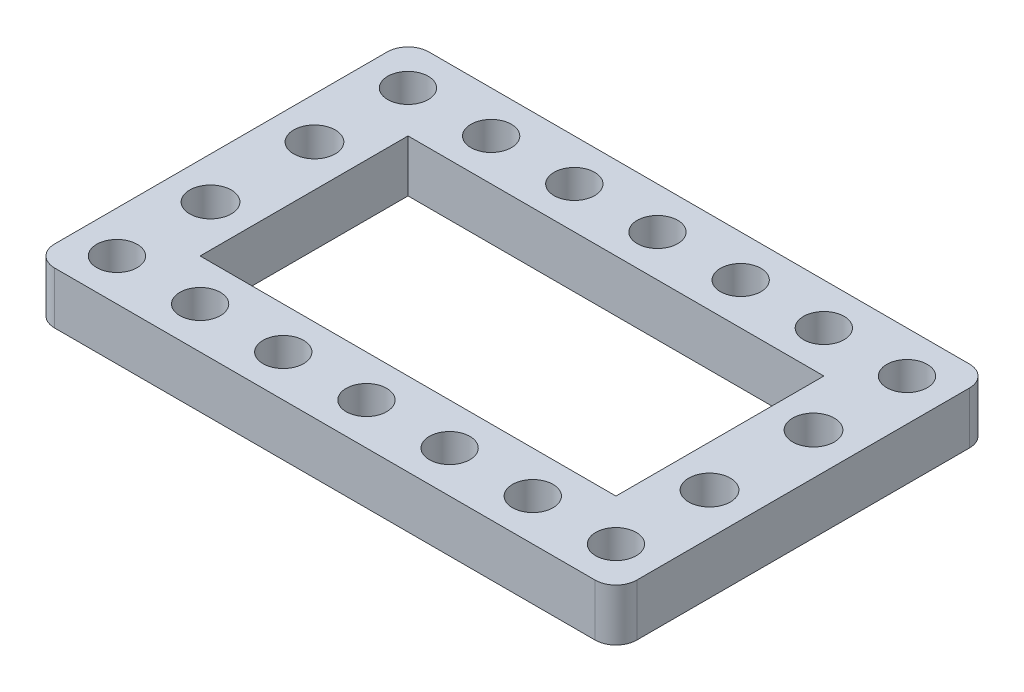
SolidWorks part; units mm, degrees
other "Markup1"
sketch "Sketch6" plane through (78, 5, 36) normal (0.7831, 0.6182, 0.0676) x (0.6216, -0.7756, -0.1096)
ref_plane "Front Plane" through (0, 0, 0) normal (0, 0, 1) x (1, 0, 0)
ref_plane "Top Plane" through (0, 0, 0) normal (0, 1, 0) x (1, 0, 0)
ref_plane "Right Plane" through (0, 0, 0) normal (1, 0, 0) x (0, 0, -1)
sketch "Sketch1" plane through (0, 0, 0) normal (0, 1, 0) x (1, 0, 0)
  line L1 (2, 0) -> (98, 0)
  line L2 (0, -2) -> (0, -34)
  line L3 (2, -36) -> (98, -36)
  line L4 (100, -2) -> (100, -34)
  arc A0 (98, -36) -> (100, -34) centre (98, -34) ccw
  arc A1 (0, -34) -> (2, -36) centre (2, -34) ccw
  arc A2 (2, 0) -> (0, -2) centre (2, -2) ccw
  arc A3 (98, 0) -> (100, -2) centre (98, -2) cw
  point P7 (100, -36)
  point P12 (0, 0)
  point P15 (100, 0)
  dimension "D3" = 2
  dimension "D1" = 100
  dimension "D2" = 36
extrude "Boss-Extrude1" add sketch "Sketch1" along normal blind 5
sketch "Sketch2" plane through (0, 5, 0) normal (0, 1, 0) x (1, 0, 0)
  line L1 (100, -34) -> (100, -2) construction
  line L2 (90, -4.0048) -> (0, -4.0048) construction
  line L3 (0, -2) -> (0, -34) construction
  line L4 (90, -32) -> (0, -32) construction
  line L6 (30, -18) -> (70, -18) construction
  line L7 (30, -8) -> (70, -8)
  line L8 (30, -8) -> (30, -28)
  line L9 (30, -28) -> (70, -28)
  line L10 (70, -8) -> (70, -28)
  line L11 (98, 0) -> (2, 0) construction
  line L12 (2, -36) -> (98, -36) construction
  line L13 (50, -8) -> (50, -28) construction
  circle A0 centre (90, -4.0048) radius 1.95
  circle A1 centre (82, -4.0048) radius 1.95
  circle A2 centre (18, -4.0048) radius 1.95
  circle A3 centre (26, -4.0048) radius 1.95
  circle A4 centre (34, -4.0048) radius 1.95
  circle A5 centre (42, -4.0048) radius 1.95
  circle A6 centre (50, -4.0048) radius 1.95
  circle A7 centre (58, -4.0048) radius 1.95
  circle A8 centre (66, -4.0048) radius 1.95
  circle A9 centre (74, -4.0048) radius 1.95
  circle A10 centre (90, -32) radius 1.95
  circle A11 centre (82, -32) radius 1.95
  circle A12 centre (18, -32) radius 1.95
  circle A13 centre (26, -32) radius 1.95
  circle A14 centre (34, -32) radius 1.95
  circle A15 centre (42, -32) radius 1.95
  circle A16 centre (50, -32) radius 1.95
  circle A17 centre (58, -32) radius 1.95
  circle A18 centre (66, -32) radius 1.95
  circle A19 centre (74, -32) radius 1.95
  dimension "D1" = 3.9
  dimension "D4" = 3.9
  dimension "D7" = 3.9
  dimension "D8" = 3.9
  dimension "D9" = 3.9
  dimension "D10" = 3.9
  dimension "D11" = 3.9
  dimension "D12" = 3.9
  dimension "D13" = 3.9
  dimension "D14" = 3.9
  dimension "D22" = 3.9
  dimension "D23" = 3.9
  dimension "D25" = 3.9
  dimension "D26" = 3.9
  dimension "D27" = 3.9
  dimension "D28" = 3.9
  dimension "D29" = 3.9
  dimension "D30" = 3.9
  dimension "D31" = 3.9
  dimension "D32" = 3.9
  dimension "D5" = 8
  dimension "D6" = 18
  dimension "D15" = 8
  dimension "D16" = 8
  dimension "D17" = 8
  dimension "D18" = 8
  dimension "D19" = 8
  dimension "D20" = 8
  dimension "D21" = 8
  dimension "D24" = 8
  dimension "D33" = 8
  dimension "D34" = 8
  dimension "D35" = 8
  dimension "D36" = 8
  dimension "D37" = 8
  dimension "D38" = 8
  dimension "D39" = 8
  dimension "D40" = 4.0048
  dimension "D41" = 10
  dimension "D43" = 40
  dimension "D44" = 20
  dimension "D46" = 4
  dimension "D47" = 10
extrude "Cut-Extrude1" cut sketch "Sketch2" against normal through all
sketch "Sketch4" plane through (0, 5, 0) normal (0, 1, 0) x (1, 0, 0)
  line L0 (98, 0) -> (2, 0) construction
  line L1 (78, 0) -> (100, 0)
  line L2 (78, 0) -> (78, -36)
  line L3 (78, -36) -> (100, -36)
  line L4 (100, 0) -> (100, -36)
  line L5 (2, -36) -> (98, -36) construction
  line L6 (100, -34) -> (100, -2) construction
  line L8 (0, 0) -> (22, 0)
  line L9 (0, 0) -> (0, -36)
  line L10 (0, -36) -> (22, -36)
  line L11 (22, 0) -> (22, -36)
  dimension "D1" = 22
  dimension "D2" = 22
extrude "Cut-Extrude2" cut sketch "Sketch4" against normal blind 10
fillet "Fillet1" radius 2 1 edges at (22, 2.5, 0)
fillet "Fillet2" radius 2 1 edges at (22, 2.5, 36)
fillet "Fillet3" radius 2 1 edges at (78, 2.5, 36)
fillet "Fillet4" radius 2 1 edges at (78, 2.5, 0)
sketch "Sketch5" plane through (0, 5, 0) normal (0, 1, 0) x (1, 0, 0)
  line L0 (22, -18) -> (78, -18) construction
  line L1 (78, -2) -> (78, -34) construction
  line L3 (70, -8) -> (30, -8) construction
  line L4 (22, -34) -> (22, -2) construction
  line L5 (74, -13) -> (74, -23) construction
  line L6 (26, -13) -> (26, -23) construction
  line L7 (30, -8) -> (30, -28) construction
  line L8 (70, -28) -> (70, -8) construction
  line L9 (30, -28) -> (70, -28) construction
  circle A0 centre (74, -13) radius 2
  circle A1 centre (74, -23) radius 2
  circle A2 centre (26, -13) radius 2
  circle A3 centre (26, -23) radius 2
  point P17 (74, -18)
  point P18 (26, -18)
  dimension "D1" = 4
  dimension "D4" = 4
  dimension "D7" = 4
  dimension "D8" = 4
  dimension "D2" = 4
  dimension "D3" = 4
  dimension "D5" = 10
  dimension "D6" = 4
  dimension "D9" = 10
  dimension "D10" = 4
extrude "Cut-Extrude3" cut sketch "Sketch5" against normal through all
